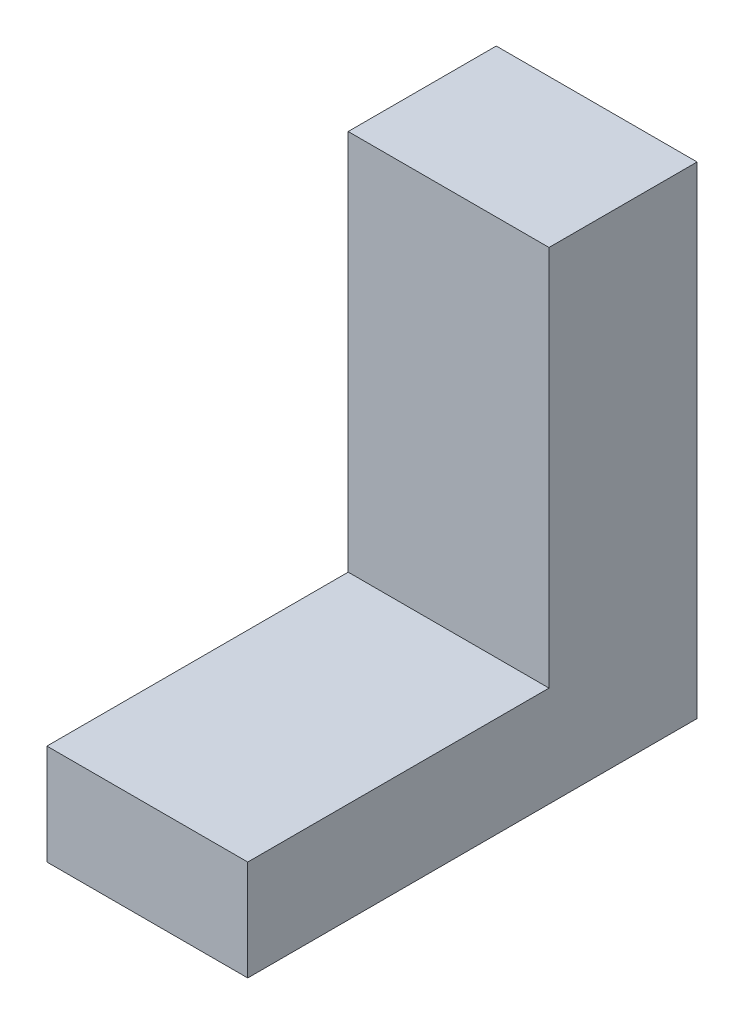
SolidWorks part; units mm, degrees
ref_plane "Front Plane" through (0, 0, 0) normal (0, 0, 1) x (1, 0, 0)
ref_plane "Top Plane" through (0, 0, 0) normal (0, 1, 0) x (1, 0, 0)
ref_plane "Right Plane" through (0, 0, 0) normal (1, 0, 0) x (0, 0, -1)
sketch "Sketch1" plane through (0, 0, 0) normal (1, 0, 0) x (0, 0, -1)
  line L1 (0, 0) -> (-762, 0)
  line L3 (0, -254) -> (-762, -254)
  line L4 (-762, 0) -> (-762, -254)
  line L5 (0, -254) -> (374.5424, -254)
  line L6 (0, 0) -> (0, 965.2)
  line L7 (0, 965.2) -> (374.5424, 965.2)
  line L8 (374.5424, -254) -> (374.5424, 965.2)
  dimension "D1" = 762
  dimension "D2" = 1219.2
  dimension "D3" = 254
  dimension "D4" = 374.5424
  dimension "D5" = 762
extrude "Boss-Extrude1" add sketch "Sketch1" along normal blind 508
